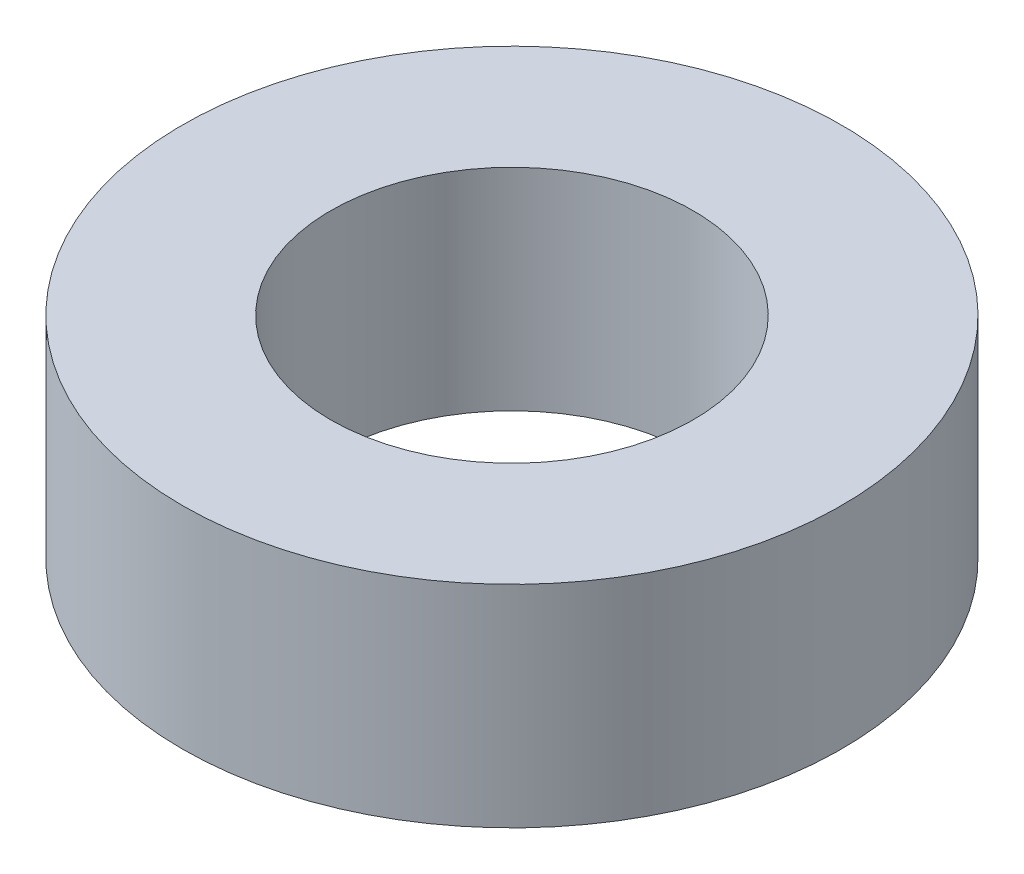
SolidWorks part; units mm, degrees
ref_plane "Plano frontal" through (0, 0, 0) normal (0, 0, 1) x (1, 0, 0)
ref_plane "Plano superior" through (0, 0, 0) normal (0, 1, 0) x (1, 0, 0)
ref_plane "Plano direito" through (0, 0, 0) normal (1, 0, 0) x (0, 0, -1)
sketch "Sketch1" plane through (0, 0, 0) normal (0, 1, 0) x (1, 0, 0)
  circle A0 centre (0, 0) radius 5
  circle A1 centre (0, 0) radius 2.75
  dimension "D1" = 10
  dimension "D2" = 5.5
extrude "Boss-Extrude1" add sketch "Sketch1" along normal mid plane 3.2
